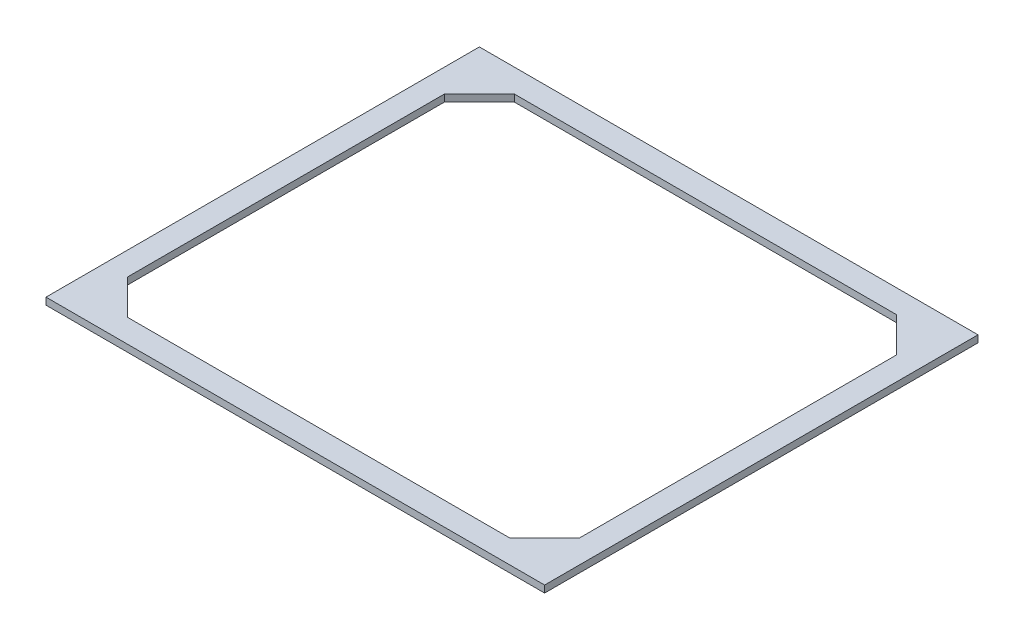
SolidWorks part; units mm, degrees
ref_plane "Front Plane" through (0, 0, 0) normal (0, 0, 1) x (1, 0, 0)
ref_plane "Top Plane" through (0, 0, 0) normal (0, 1, 0) x (1, 0, 0)
ref_plane "Right Plane" through (0, 0, 0) normal (1, 0, 0) x (0, 0, -1)
sketch "Sketch1" plane through (0, 0, 0) normal (0, 1, 0) x (1, 0, 0)
  line L0 (-82, 83) -> (82, 83)
  line L1 (-107, -93) -> (107, -93)
  line L2 (-107, -93) -> (-107, 93)
  line L3 (-107, 93) -> (107, 93)
  line L4 (107, -93) -> (107, 93)
  line L5 (97, -68) -> (97, 68)
  line L6 (-82, -83) -> (82, -83)
  line L7 (-97, -68) -> (-97, 68)
  line L8 (97, -83) -> (97, 83) construction
  line L9 (-97, -83) -> (97, -83) construction
  line L10 (82, -83) -> (97, -68)
  line L11 (-97, 83) -> (97, 83) construction
  line L12 (82, 83) -> (97, 68)
  line L13 (-97, -83) -> (-97, 83) construction
  line L14 (-97, 68) -> (-82, 83)
  line L15 (-97, -68) -> (-82, -83)
  dimension "D1" = 214
  dimension "D2" = 186
  dimension "D3" = 10
extrude "Boss-Extrude1" add sketch "Sketch1" along normal blind 3
